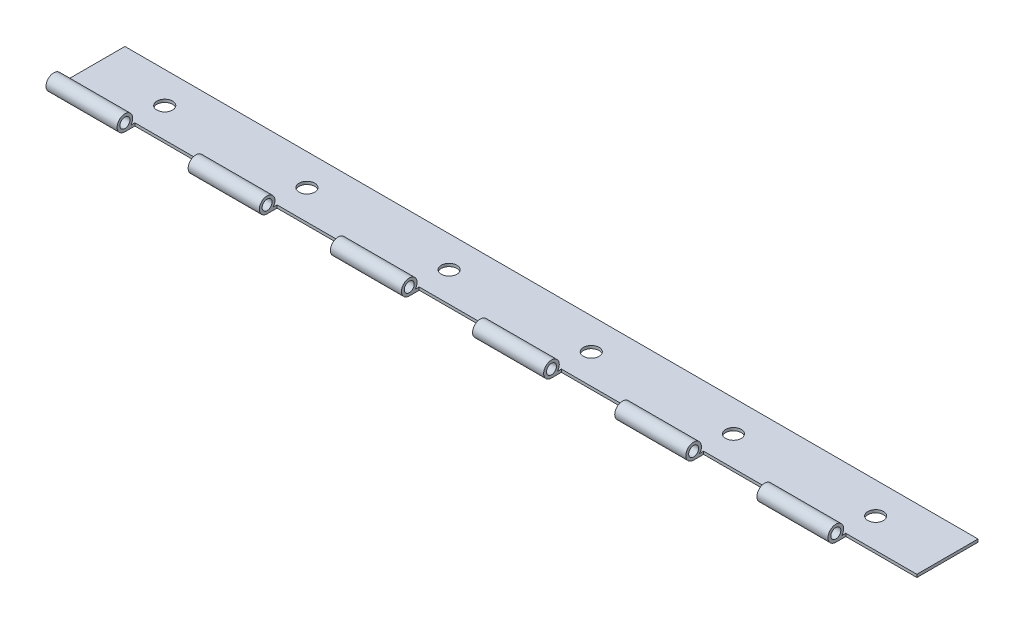
SolidWorks part; units mm, degrees
ref_plane "Front Plane" through (0, 0, 0) normal (0, 0, 1) x (1, 0, 0)
ref_plane "Top Plane" through (0, 0, 0) normal (0, 1, 0) x (1, 0, 0)
ref_plane "Right Plane" through (0, 0, 0) normal (1, 0, 0) x (0, 0, -1)
sketch "Sketch1" plane through (0, 0, 0) normal (1, 0, 0) x (0, 0, -1)
  line L0 (0, -2.794) -> (25.4, -2.794)
  line L1 (25.4, -2.794) -> (25.4, -1.778)
  line L2 (25.4, -1.778) -> (2.1553, -1.778)
  circle A0 centre (0, 0) radius 1.778
  arc A1 (2.1553, -1.778) -> (0, -2.794) centre (0, 0) ccw
  dimension "D1" = 3.556
  dimension "D2" = 5.588
  dimension "D3" = 1.016
  dimension "D4" = 25.4
extrude "Boss-Extrude1" add sketch "Sketch1" along normal mid plane 304.8 contours L0 L1 L2 A1 | A0
sketch "Sketch2" plane through (0, -1.778, 0) normal (0, 1, 0) x (1, 0, 0)
  line L0 (152.4, 25.4) -> (-152.4, 25.4) construction
  line L1 (-152.4, -2.794) -> (152.4, -2.794) construction
  line L2 (-25.4, -2.794) -> (0, -2.794)
  line L3 (-25.4, -2.794) -> (-25.4, 3.556)
  line L4 (-25.4, 3.556) -> (0, 3.556)
  line L5 (0, -2.794) -> (0, 3.556)
  circle A0 centre (-25.4, 14.224) radius 2.794
  dimension "D1" = 5.588
  dimension "D3" = 25.4
  dimension "D2" = 11.176
  dimension "D4" = 6.35
  dimension "D5" = 25.4
extrude "Cut-Extrude1" cut sketch "Sketch2" against normal mid plane 1828.8
pattern_linear "LPattern1" count 4 spacing 50.8 along (-1, 0, 0) of "Cut-Extrude1"
pattern_linear "LPattern2" count 4 spacing 50.8 along (1, 0, 0) of "Cut-Extrude1"
equation "\"HingeLength\"=12"
equation "\"HoleSpace\"= 2"
equation "\"CutLength\"= 1"
equation "\"D1@Boss-Extrude1\"=\"HingeLength\""
equation "\"D3@Sketch2\"=\"HoleSpace\"/2"
equation "\"D5@Sketch2\"=\"CutLength\""
equation "\"D3@LPattern1\"=\"HoleSpace\""
equation "\"D1@LPattern1\"=((\"HingeLength\"/2)/\"HoleSpace\")+1"
equation "\"D3@LPattern2\"=\"HoleSpace\""
equation "\"D1@LPattern2\"=((\"HingeLength\"/2)/\"HoleSpace\")+1"
